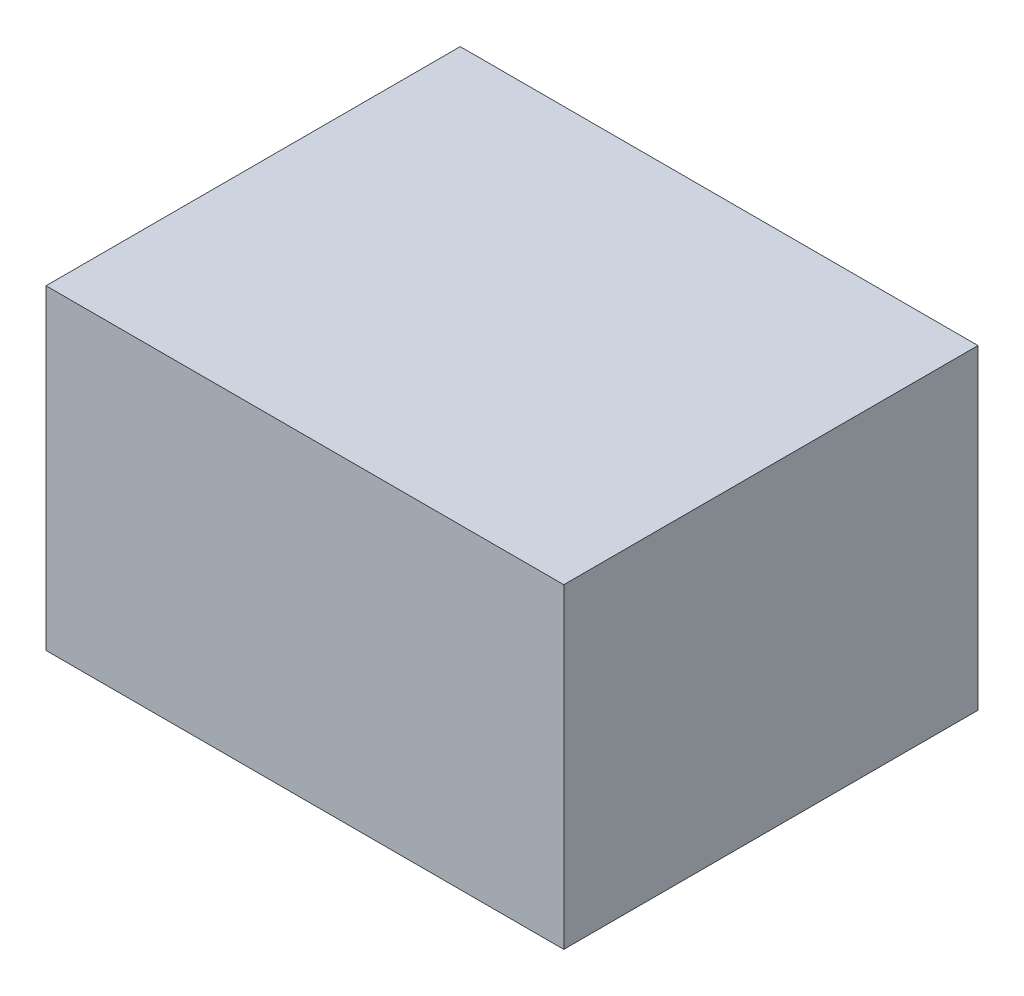
SolidWorks part; units mm, degrees
ref_plane "Front Plane" through (0, 0, 0) normal (0, 0, 1) x (1, 0, 0)
ref_plane "Top Plane" through (0, 0, 0) normal (0, 1, 0) x (1, 0, 0)
ref_plane "Right Plane" through (0, 0, 0) normal (1, 0, 0) x (0, 0, -1)
sketch "Sketch1" plane through (0, 0, 0) normal (0, 1, 0) x (1, 0, 0)
  line L0 (-2.5, 2) -> (2.5, -2) construction
  line L1 (-2.5, 2) -> (2.5, 2)
  line L2 (-2.5, 2) -> (-2.5, -2)
  line L3 (-2.5, -2) -> (2.5, -2)
  line L4 (2.5, 2) -> (2.5, -2)
  dimension "D1" = 5
  dimension "D2" = 4
extrude "Boss-Extrude1" add sketch "Sketch1" along normal blind 3.05
